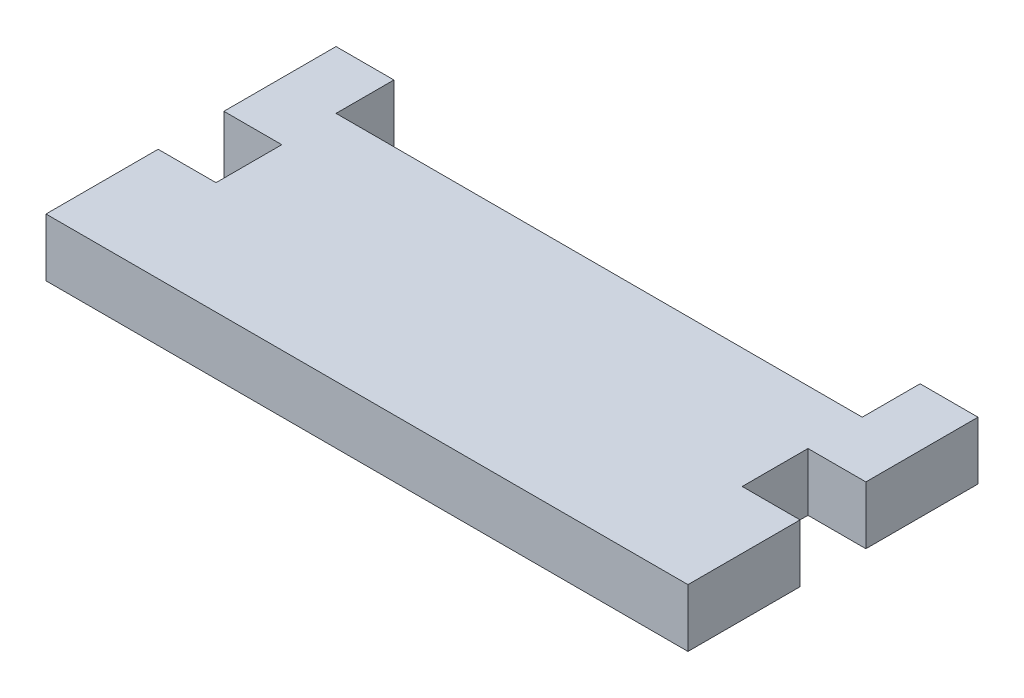
SolidWorks part; units mm, degrees
material "Acrylic (Medium-high impact)"
ref_plane "Front Plane" through (0, 0, 0) normal (0, 0, 1) x (1, 0, 0)
ref_plane "Top Plane" through (0, 0, 0) normal (0, 1, 0) x (1, 0, 0)
ref_plane "Right Plane" through (0, 0, 0) normal (1, 0, 0) x (0, 0, -1)
sketch "Sketch1" plane through (0, 0, 0) normal (0, 1, 0) x (1, 0, 0)
  line L1 (-30.988, 14) -> (30.988, 14)
  line L2 (-30.988, 14) -> (-30.988, -14)
  line L3 (-30.988, -14) -> (30.988, -14)
  line L4 (30.988, 14) -> (30.988, -14)
  line L5 (-30.988, 14) -> (30.988, -14) construction
  line L6 (-30.988, -14) -> (30.988, 14) construction
  line L7 (-25.4, 14) -> (25.4, 14)
  line L8 (-25.4, 14) -> (-25.4, 8.412)
  line L9 (-25.4, 8.412) -> (25.4, 8.412)
  line L10 (25.4, 14) -> (25.4, 8.412)
  line L11 (30.988, 3.175) -> (25.4, 3.175)
  line L12 (30.988, 3.175) -> (30.988, -3.175)
  line L13 (30.988, -3.175) -> (25.4, -3.175)
  line L14 (25.4, 3.175) -> (25.4, -3.175)
  line L15 (-30.988, 3.175) -> (-25.4, 3.175)
  line L16 (-30.988, 3.175) -> (-30.988, -3.175)
  line L17 (-30.988, -3.175) -> (-25.4, -3.175)
  line L18 (-25.4, 3.175) -> (-25.4, -3.175)
  point P0 (0, 0)
  point P18 (0, 8.412)
  point P19 (-25.4, 0)
  point P20 (25.4, 0)
  dimension "D1" = 61.976
  dimension "D2" = 28
  dimension "D3" = 50.8
  dimension "D4" = 5.588
  dimension "D5" = 5.588
  dimension "D6" = 6.35
extrude "Boss-Extrude1" add sketch "Sketch1" along normal blind 5.588 contours L15 L18 L17 L2 L3 L4 L13 L14 L11 L1 L10 L9 L8
